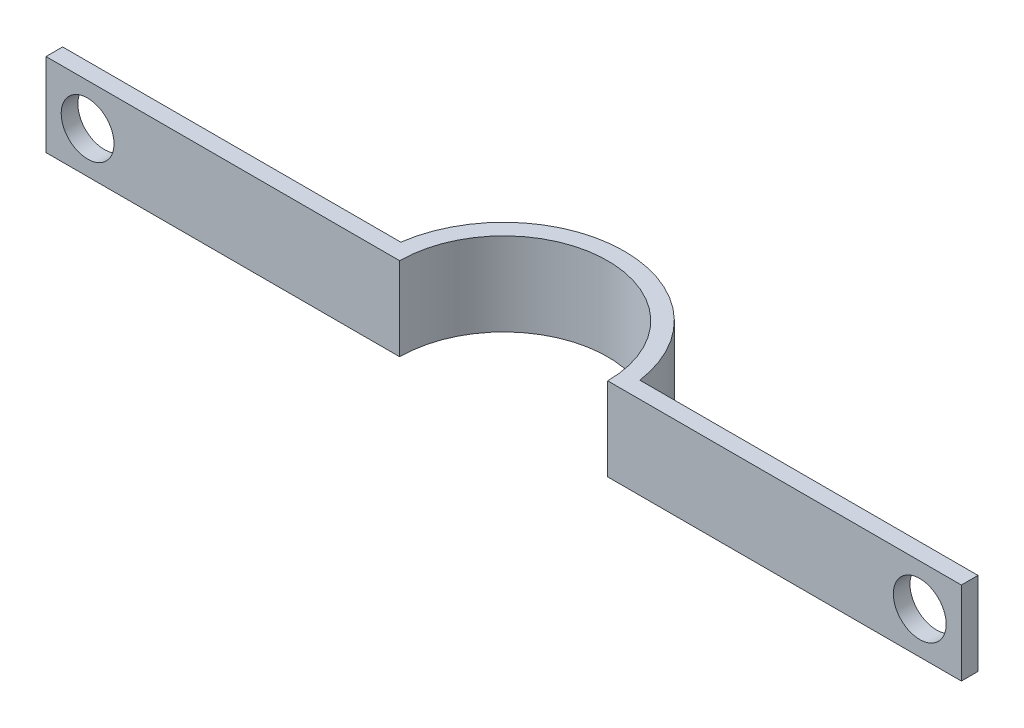
SolidWorks part; units mm, degrees
ref_plane "Front Plane" through (0, 0, 0) normal (0, 0, 1) x (1, 0, 0)
ref_plane "Top Plane" through (0, 0, 0) normal (0, 1, 0) x (1, 0, 0)
ref_plane "Right Plane" through (0, 0, 0) normal (1, 0, 0) x (0, 0, -1)
ref_plane "Plane1" through (0, -10, 0) normal (0, -1, 0) x (1, 0, 0)
sketch "Sketch1" plane through (0, -10, 0) normal (0, -1, 0) x (1, 0, 0)
  line L0 (55, 0) -> (-55, 0)
  line L1 (-55, 0) -> (-55, -2)
  line L2 (-55, -2) -> (-14.3614, -2)
  line L3 (14.3614, -2) -> (55, -2)
  line L4 (55, -2) -> (55, 0)
  arc A0 (-14.3614, -2) -> (14.3614, -2) centre (0, 0) ccw
extrude "Boss-Extrude1" add sketch "Sketch1" against normal blind 10
hole_wizard "Hole1" positions "Sketch3" profile "Sketch2" legacy
sketch "Sketch3" plane through (0, 0, -2) normal (0, 0, -1) x (-1, 0, 0)
  point P0 (-50, -5)
  point P1 (50, -5)
sketch "Sketch2" plane through (50, -5, -2) normal (1, 0, 0) x (0, 1, 0)
  line L0 (0, 0) -> (0, 2)
  line L1 (0, 2) -> (3.175, 2)
  line L2 (3.175, 2) -> (3.175, 0)
  line L3 (3.175, 0) -> (0, 0)
  line L4 (0, 110) -> (0, -10) construction
  dimension "Diameter" = 6.35
  dimension "Depth" = 2
hole_wizard "Ø25.0 (25) Diameter Hole1" positions "Sketch5" profile "Sketch4" hole size "Ø25.0" standard "ANSI Metric"
sketch "Sketch5" plane through (0, -10, 0) normal (0, -1, 0) x (-1, 0, 0)
  point P0 (0, 0)
sketch "Sketch4" plane through (0, -10, 0) normal (1, 0, 0) x (0, 0, -1)
  line L0 (0, 0) -> (0, 10)
  line L1 (0, 10) -> (12.5, 10)
  line L2 (12.5, 10) -> (12.5, 0)
  line L5 (12.5, 0) -> (0, 0)
  line L11 (0, -6.35) -> (0, 107.95) construction
  dimension "Thru Hole Dia." = 25
  dimension "Thru Hole Depth" = 10
scale "Scale1" scale about centroid uniform scaling yes scale factor 4
